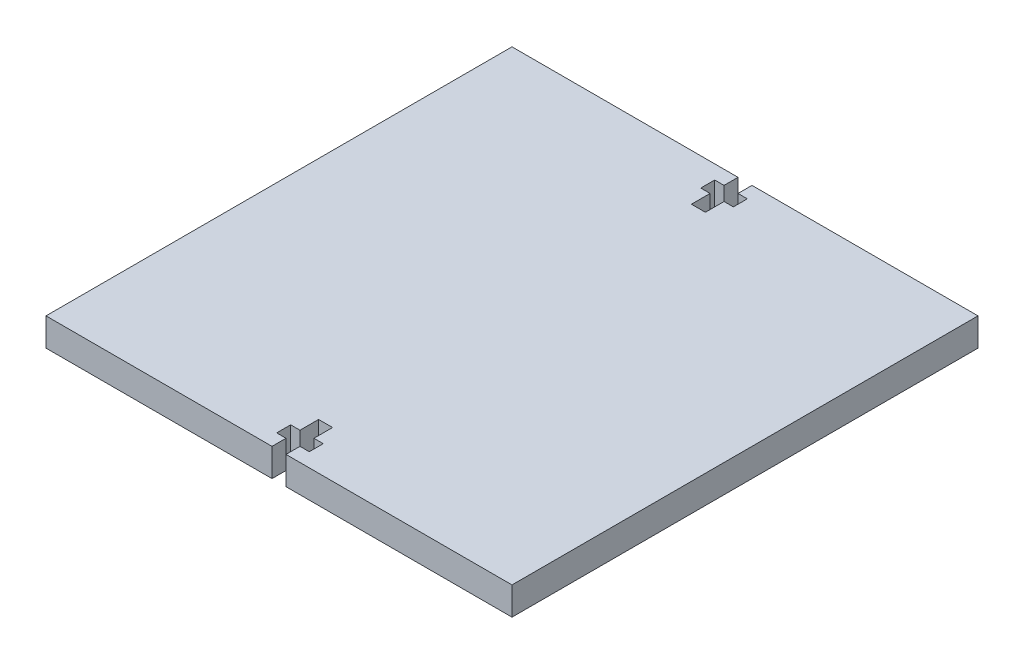
SolidWorks part; units mm, degrees
ref_plane "Front Plane" through (0, 0, 0) normal (0, 0, 1) x (1, 0, 0)
ref_plane "Top Plane" through (0, 0, 0) normal (0, 1, 0) x (1, 0, 0)
ref_plane "Right Plane" through (0, 0, 0) normal (1, 0, 0) x (0, 0, -1)
sketch "Sketch2" plane through (0, 0, 0) normal (0, 1, 0) x (1, 0, 0)
  line L0 (0, 0) -> (-100, 0)
  line L1 (-100, 0) -> (-100, 100)
  line L2 (-100, 100) -> (0, 100)
  line L3 (0, 100) -> (0, 0)
extrude "Boss-Extrude1" add sketch "Sketch2" along normal blind 6 contours L2 L3 L0 L1
sketch "Sketch3" plane through (0, 6, 0) normal (0, 1, 0) x (1, 0, 0)
  line L0 (-50, 100) -> (-50, 0) construction
  line L1 (-100, 100) -> (0, 100) construction
  line L2 (0, 0) -> (-100, 0) construction
  line L3 (-100, 50) -> (0, 50) construction
  line L4 (-100, 0) -> (-100, 100) construction
  line L5 (0, 100) -> (0, 0) construction
  line L6 (-50, 100) -> (-48.5, 100)
  line L7 (-48.5, 100) -> (-48.5, 97)
  line L8 (-48.5, 97) -> (-46.5, 97)
  line L9 (-46.5, 97) -> (-46.5, 94)
  line L10 (-46.5, 94) -> (-48.5, 94)
  line L11 (-48.5, 94) -> (-48.5, 90)
  line L12 (-48.5, 90) -> (-50, 90)
  line L13 (-50, 100) -> (-51.5, 100)
  line L14 (-51.5, 100) -> (-51.5, 97)
  line L15 (-51.5, 97) -> (-53.5, 97)
  line L16 (-53.5, 97) -> (-53.5, 94)
  line L17 (-53.5, 94) -> (-51.5, 94)
  line L18 (-51.5, 94) -> (-51.5, 90)
  line L19 (-51.5, 90) -> (-50, 90)
  line L20 (-50, 0) -> (-48.5, 0)
  line L21 (0, 0) -> (-100, 0) construction
  line L22 (-48.5, 0) -> (-48.5, 3)
  line L23 (-48.5, 3) -> (-46.5, 3)
  line L24 (-46.5, 3) -> (-46.5, 6)
  line L25 (-46.5, 6) -> (-48.5, 6)
  line L26 (-48.5, 6) -> (-48.5, 10)
  line L27 (-48.5, 10) -> (-50, 10)
  line L28 (-50, 10) -> (-51.5, 10)
  line L29 (-51.5, 10) -> (-51.5, 6)
  line L30 (-51.5, 6) -> (-53.5, 6)
  line L31 (-53.5, 6) -> (-53.5, 3)
  line L32 (-53.5, 3) -> (-51.5, 3)
  line L35 (-51.5, 3) -> (-51.5, 0)
  line L36 (-51.5, 0) -> (-50, 0)
extrude "Cut-Extrude1" cut sketch "Sketch3" against normal through all
